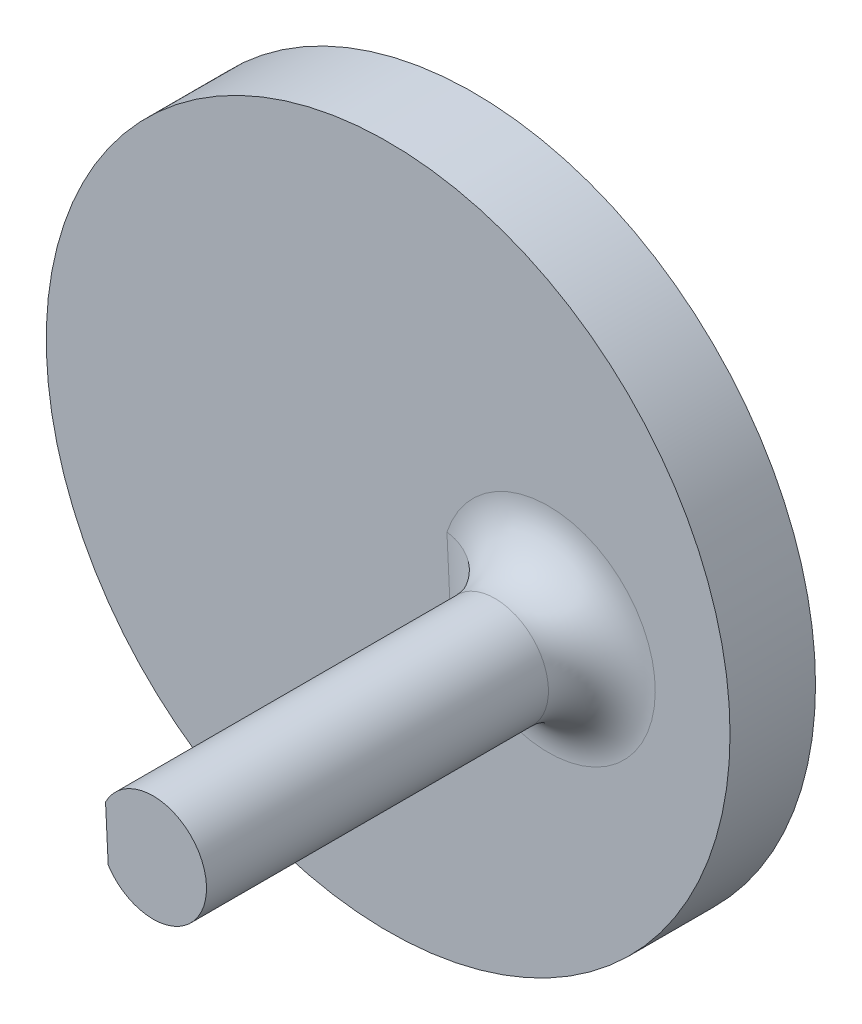
SolidWorks part; units mm, degrees
material "ABS"
ref_plane "Plan de face" through (0, 0, 0) normal (0, 0, 1) x (1, 0, 0)
ref_plane "Plan de dessus" through (0, 0, 0) normal (0, 1, 0) x (1, 0, 0)
ref_plane "Plan de droite" through (0, 0, 0) normal (1, 0, 0) x (0, 0, -1)
sketch "Esquisse1" plane through (0, 0, 0) normal (0, 0, 1) x (1, 0, 0)
  circle A0 centre (0, 0) radius 20.32
  circle A1 centre (0, 0) radius 9.525 construction
  circle A2 centre (9.525, 0) radius 3.175
  circle A3 centre (0, 0) radius 3.175
  dimension "D1" = 40.64
  dimension "D2" = 19.05
  dimension "D3" = 6.35
  dimension "D4" = 6.35
extrude "Boss.-Extru.1" add sketch "Esquisse1" along normal blind 5.08
sketch "Esquisse2" plane through (0, 0, 0) normal (0, 0, 1) x (1, 0, 0)
  circle A0 centre (9.525, 0) radius 3.175
  circle A1 centre (9.525, 0) radius 3.175 construction
extrude "Boss.-Extru.2" add sketch "Esquisse2" along normal blind 28.575
sketch "Esquisse3" plane through (0, 0, 28.575) normal (0, 0, 1) x (1, 0, 0)
  line L0 (6.8583, -1.7232) -> (6.6993, 1.4478)
  circle A0 centre (9.525, 0) radius 3.175 construction
  circle A1 centre (9.525, 0) radius 3.175
  circle M3 centre (9.525, 0) radius 3.175
  dimension "D1" = 3.175
extrude "Enlèv. mat.-Extru.1" cut sketch "Esquisse3" against normal up to surface (23.495 mm away) contours L0 M3
sketch "Esquisse4" plane through (0, 0, 5.08) normal (0, 0, 1) x (1, 0, 0)
  circle A0 centre (0, 0) radius 4.0978
extrude "Boss.-Extru.3" add sketch "Esquisse4" against normal up to surface (5.08 mm away) up to face at (20.32, 0, 0)
sketch "Esquisse5" plane through (0, 0, 0) normal (0, 0, -1) x (-1, 0, 0)
  circle A0 centre (0, 0) radius 3.175
  circle A1 centre (0, 0) radius 9.525
  dimension "D1" = 19.05
  dimension "D2" = 6.35
extrude "Boss.-Extru.4" add sketch "Esquisse5" along normal blind 6.35
fillet "Congé1" radius 3.175 3 edges at (12.696, 0.159, 5.08) (6.7788, -0.1377, 5.08) (9.525, 0, 0)
